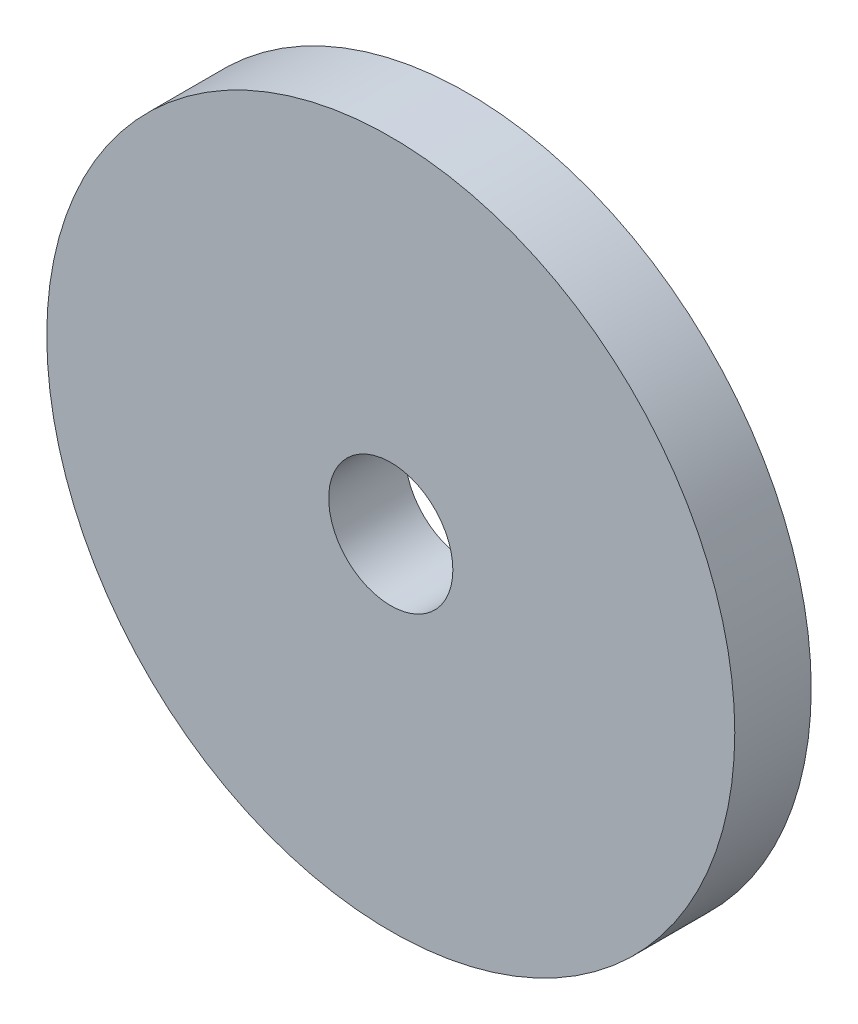
SolidWorks part; units mm, degrees
material "304 SSTL"
ref_plane "XY" through (0, 0, 0) normal (0, 0, 1) x (1, 0, 0)
ref_plane "XZ" through (0, 0, 0) normal (0, 1, 0) x (1, 0, 0)
ref_plane "YZ" through (0, 0, 0) normal (1, 0, 0) x (0, 0, -1)
sketch "Sketch1" plane through (0, 0, 0) normal (0, 0, 1) x (1, 0, 0)
  circle A0 centre (0, 0) radius 28.575
  circle A1 centre (0, 0) radius 5.1562
  dimension "D1" = 10.3124
  dimension "D2" = 57.15
extrude "Extrude1" add sketch "Sketch1" along normal blind 6.35
